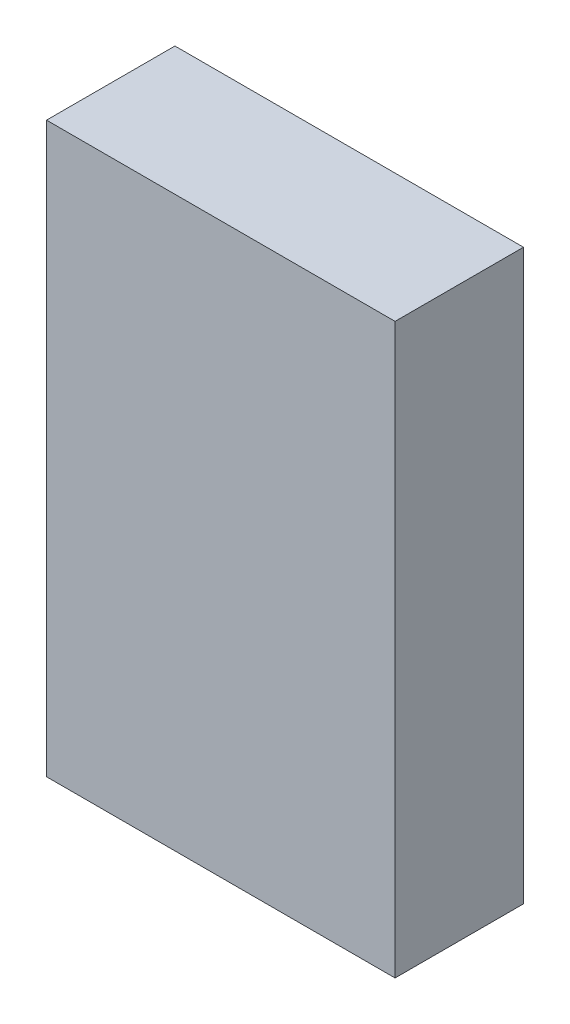
SolidWorks part; units mm, degrees
ref_plane "Front Plane" through (0, 0, 0) normal (0, 0, 1) x (1, 0, 0)
ref_plane "Top Plane" through (0, 0, 0) normal (0, 1, 0) x (1, 0, 0)
ref_plane "Right Plane" through (0, 0, 0) normal (1, 0, 0) x (0, 0, -1)
sketch "Sketch1" plane through (0, 0, 0) normal (0, 0, 1) x (1, 0, 0)
  line L1 (-19, -31) -> (19, -31)
  line L2 (-19, -31) -> (-19, 31)
  line L3 (-19, 31) -> (19, 31)
  line L4 (19, -31) -> (19, 31)
  line L5 (-19, -31) -> (19, 31) construction
  line L6 (-19, 31) -> (19, -31) construction
  point P0 (0, 0)
  dimension "D1" = 62
  dimension "D2" = 38
extrude "Boss-Extrude1" add sketch "Sketch1" along normal blind 14
